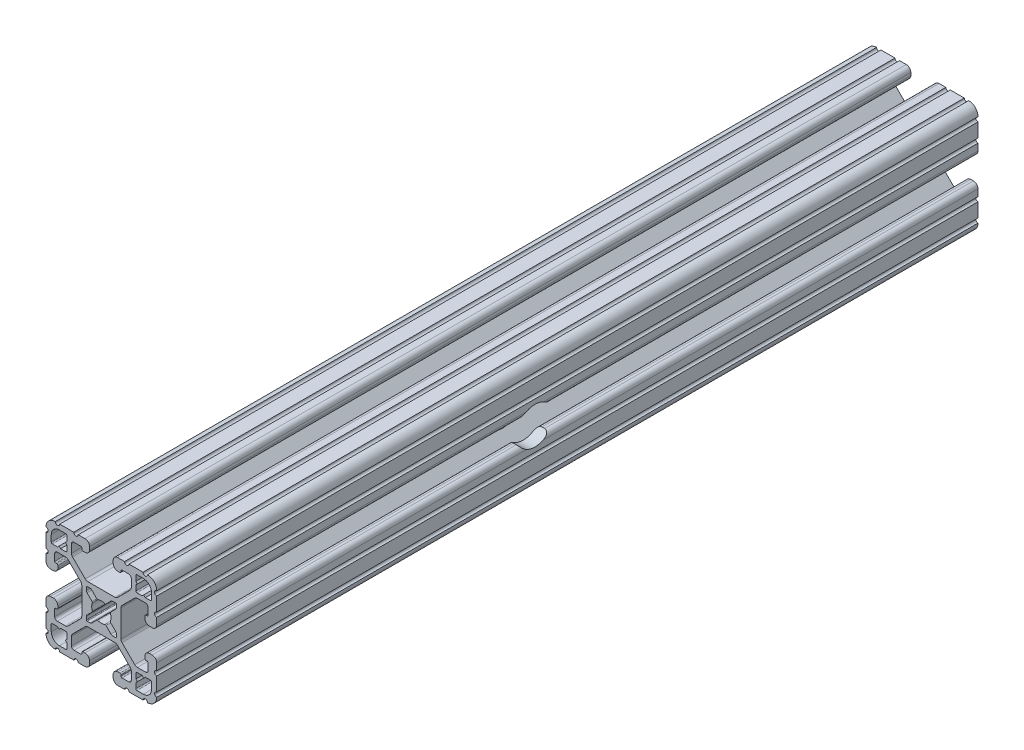
SolidWorks part; units mm, degrees
ref_plane "Front Plane" through (0, 0, 0) normal (0, 0, 1) x (1, 0, 0)
ref_plane "Top Plane" through (0, 0, 0) normal (0, 1, 0) x (1, 0, 0)
ref_plane "Right Plane" through (0, 0, 0) normal (1, 0, 0) x (0, 0, -1)
ref_plane "Plane1" through (0, 0, -2322.576) normal (0, 0, -1) x (-1, 0, 0)
sketch "Sketch1" plane through (0, 0, -2322.576) normal (0, 0, -1) x (-1, 0, 0)
  line L0 (17.2466, 14.4526) -> (17.2466, 12.2428)
  line L1 (16.8656, 11.8618) -> (15.0927, 11.8618)
  line L2 (15.0927, 11.8618) -> (14.5542, 12.4003)
  line L3 (14.5542, 12.4003) -> (14.0157, 11.8618)
  line L4 (14.0157, 11.8618) -> (12.2428, 11.8618)
  line L5 (11.8618, 12.2428) -> (11.8618, 14.0157)
  line L6 (11.8618, 14.0157) -> (12.4003, 14.5542)
  line L7 (12.4003, 14.5542) -> (11.8618, 15.0927)
  line L8 (11.8618, 15.0927) -> (11.8618, 16.8656)
  line L9 (12.2428, 17.2466) -> (14.4526, 17.2466)
  line L10 (17.2466, -12.2428) -> (17.2466, -14.4526)
  line L11 (14.4526, -17.2466) -> (12.2428, -17.2466)
  line L12 (11.8618, -16.8656) -> (11.8618, -15.0927)
  line L13 (11.8618, -15.0927) -> (12.4003, -14.5542)
  line L14 (12.4003, -14.5542) -> (11.8618, -14.0157)
  line L15 (11.8618, -14.0157) -> (11.8618, -12.2428)
  line L16 (12.2428, -11.8618) -> (14.0157, -11.8618)
  line L17 (14.0157, -11.8618) -> (14.5542, -12.4003)
  line L18 (14.5542, -12.4003) -> (15.0927, -11.8618)
  line L19 (15.0927, -11.8618) -> (16.8656, -11.8618)
  line L20 (5.1689, -3.9207) -> (5.1689, -4.9149)
  line L21 (4.9149, -5.1689) -> (3.9207, -5.1689)
  line L22 (3.2921, -4.9085) -> (1.5823, -3.1988)
  line L23 (-1.5823, -3.1988) -> (-3.2921, -4.9085)
  line L24 (-3.9207, -5.1689) -> (-4.9149, -5.1689)
  line L25 (-5.1689, -4.9149) -> (-5.1689, -3.9207)
  line L26 (-4.9085, -3.2921) -> (-3.1988, -1.5823)
  line L27 (-3.1988, 1.5823) -> (-4.9085, 3.2921)
  line L28 (-5.1689, 3.9207) -> (-5.1689, 4.9149)
  line L29 (-4.9149, 5.1689) -> (-3.9207, 5.1689)
  line L30 (-3.2921, 4.9085) -> (-1.5823, 3.1988)
  line L31 (1.5823, 3.1988) -> (3.2921, 4.9085)
  line L32 (3.9207, 5.1689) -> (4.9149, 5.1689)
  line L33 (5.1689, 4.9149) -> (5.1689, 3.9207)
  line L34 (4.9085, 3.2921) -> (3.1988, 1.5823)
  line L35 (3.1988, -1.5823) -> (4.9085, -3.2921)
  line L36 (-11.8618, -12.2428) -> (-11.8618, -14.0157)
  line L37 (-11.8618, -14.0157) -> (-12.4003, -14.5542)
  line L38 (-12.4003, -14.5542) -> (-11.8618, -15.0927)
  line L39 (-11.8618, -15.0927) -> (-11.8618, -16.8656)
  line L40 (-12.2428, -17.2466) -> (-14.4526, -17.2466)
  line L41 (-17.2466, -14.4526) -> (-17.2466, -12.2428)
  line L42 (-16.8656, -11.8618) -> (-15.0927, -11.8618)
  line L43 (-15.0927, -11.8618) -> (-14.5542, -12.4003)
  line L44 (-14.5542, -12.4003) -> (-14.0157, -11.8618)
  line L45 (-14.0157, -11.8618) -> (-12.2428, -11.8618)
  line L46 (-11.8618, 16.8656) -> (-11.8618, 15.0927)
  line L47 (-11.8618, 15.0927) -> (-12.4003, 14.5542)
  line L48 (-12.4003, 14.5542) -> (-11.8618, 14.0157)
  line L49 (-11.8618, 14.0157) -> (-11.8618, 12.2428)
  line L50 (-12.2428, 11.8618) -> (-14.0157, 11.8618)
  line L51 (-14.0157, 11.8618) -> (-14.5542, 12.4003)
  line L52 (-14.5542, 12.4003) -> (-15.0927, 11.8618)
  line L53 (-15.0927, 11.8618) -> (-16.8656, 11.8618)
  line L54 (-17.2466, 12.2428) -> (-17.2466, 14.4526)
  line L55 (-14.4526, 17.2466) -> (-12.2428, 17.2466)
  line L56 (19.05, -14.3256) -> (19.05, -9.4996)
  line L57 (19.05, -7.9756) -> (19.05, -5.6388)
  line L58 (17.4752, -4.064) -> (16.5608, -4.064)
  line L59 (14.986, -5.6388) -> (14.986, -6.35)
  line L60 (15.367, -6.731) -> (15.6972, -6.731)
  line L61 (16.0782, -7.112) -> (16.0782, -9.398)
  line L62 (15.1892, -10.287) -> (12.3756, -10.287)
  line L63 (11.4776, -9.915) -> (7.1157, -5.5531)
  line L64 (6.7437, -4.6551) -> (6.7437, 4.6551)
  line L65 (7.1157, 5.5531) -> (11.4776, 9.915)
  line L66 (12.3756, 10.287) -> (15.1892, 10.287)
  line L67 (16.0782, 9.398) -> (16.0782, 7.112)
  line L68 (15.6972, 6.731) -> (15.367, 6.731)
  line L69 (14.986, 6.35) -> (14.986, 5.6388)
  line L70 (16.5608, 4.064) -> (17.4752, 4.064)
  line L71 (19.05, 5.6388) -> (19.05, 7.9756)
  line L72 (19.05, 9.4996) -> (19.05, 14.3256)
  line L73 (14.3256, 19.05) -> (9.4996, 19.05)
  line L74 (7.9756, 19.05) -> (5.6388, 19.05)
  line L75 (4.064, 17.4752) -> (4.064, 16.5608)
  line L76 (5.6388, 14.986) -> (6.35, 14.986)
  line L77 (6.731, 15.367) -> (6.731, 15.6972)
  line L78 (7.112, 16.0782) -> (9.398, 16.0782)
  line L79 (10.287, 15.1892) -> (10.287, 12.3756)
  line L80 (9.915, 11.4776) -> (5.5531, 7.1157)
  line L81 (4.6551, 6.7437) -> (-4.6551, 6.7437)
  line L82 (-5.5531, 7.1157) -> (-9.915, 11.4776)
  line L83 (-10.287, 12.3756) -> (-10.287, 15.1892)
  line L84 (-9.398, 16.0782) -> (-7.112, 16.0782)
  line L85 (-6.731, 15.6972) -> (-6.731, 15.367)
  line L86 (-6.35, 14.986) -> (-5.6388, 14.986)
  line L87 (-4.064, 16.5608) -> (-4.064, 17.4752)
  line L88 (-5.6388, 19.05) -> (-7.9756, 19.05)
  line L89 (-9.4996, 19.05) -> (-14.3256, 19.05)
  line L90 (-19.05, 14.3256) -> (-19.05, 9.4996)
  line L91 (-19.05, 7.9756) -> (-19.05, 5.6388)
  line L92 (-17.4752, 4.064) -> (-16.5608, 4.064)
  line L93 (-14.986, 5.6388) -> (-14.986, 6.35)
  line L94 (-15.367, 6.731) -> (-15.6972, 6.731)
  line L95 (-16.0782, 7.112) -> (-16.0782, 9.398)
  line L96 (-15.1892, 10.287) -> (-12.3756, 10.287)
  line L97 (-11.4776, 9.915) -> (-7.1157, 5.5531)
  line L98 (-6.7437, 4.6551) -> (-6.7437, -4.6551)
  line L99 (-7.1157, -5.5531) -> (-11.4776, -9.915)
  line L100 (-12.3756, -10.287) -> (-15.1892, -10.287)
  line L101 (-16.0782, -9.398) -> (-16.0782, -7.112)
  line L102 (-15.6972, -6.731) -> (-15.367, -6.731)
  line L103 (-14.986, -6.35) -> (-14.986, -5.6388)
  line L104 (-16.5608, -4.064) -> (-17.4752, -4.064)
  line L105 (-19.05, -5.6388) -> (-19.05, -7.9756)
  line L106 (-19.05, -9.4996) -> (-19.05, -14.3256)
  line L107 (-14.3256, -19.05) -> (-9.4996, -19.05)
  line L108 (-7.9756, -19.05) -> (-5.6388, -19.05)
  line L109 (-4.064, -17.4752) -> (-4.064, -16.5608)
  line L110 (-5.6388, -14.986) -> (-6.35, -14.986)
  line L111 (-6.731, -15.367) -> (-6.731, -15.6972)
  line L112 (-7.112, -16.0782) -> (-9.398, -16.0782)
  line L113 (-10.287, -15.1892) -> (-10.287, -12.3756)
  line L114 (-9.915, -11.4776) -> (-5.5531, -7.1157)
  line L115 (-4.6551, -6.7437) -> (4.6551, -6.7437)
  line L116 (5.5531, -7.1157) -> (9.915, -11.4776)
  line L117 (10.287, -12.3756) -> (10.287, -15.1892)
  line L118 (9.398, -16.0782) -> (7.112, -16.0782)
  line L119 (6.731, -15.6972) -> (6.731, -15.367)
  line L120 (6.35, -14.986) -> (5.6388, -14.986)
  line L121 (4.064, -16.5608) -> (4.064, -17.4752)
  line L122 (5.6388, -19.05) -> (7.9756, -19.05)
  line L123 (9.4996, -19.05) -> (14.3256, -19.05)
  arc A0 (17.2466, 12.2428) -> (16.8656, 11.8618) centre (16.8656, 12.2428) cw
  arc A1 (12.2428, 11.8618) -> (11.8618, 12.2428) centre (12.2428, 12.2428) cw
  arc A2 (11.8618, 16.8656) -> (12.2428, 17.2466) centre (12.2428, 16.8656) cw
  arc A3 (14.4526, 17.2466) -> (17.2466, 14.4526) centre (14.4526, 14.4526) cw
  arc A4 (17.2466, -14.4526) -> (14.4526, -17.2466) centre (14.4526, -14.4526) cw
  arc A5 (12.2428, -17.2466) -> (11.8618, -16.8656) centre (12.2428, -16.8656) cw
  arc A6 (11.8618, -12.2428) -> (12.2428, -11.8618) centre (12.2428, -12.2428) cw
  arc A7 (16.8656, -11.8618) -> (17.2466, -12.2428) centre (16.8656, -12.2428) cw
  arc A8 (5.1689, -4.9149) -> (4.9149, -5.1689) centre (4.9149, -4.9149) cw
  arc A9 (3.9207, -5.1689) -> (3.2921, -4.9085) centre (3.9207, -4.2799) cw
  arc A10 (1.5823, -3.1988) -> (1.178, -3.1119) centre (1.3129, -3.4682) ccw
  arc A11 (1.178, -3.1119) -> (-1.178, -3.1119) centre (0, 0) cw
  arc A12 (-1.178, -3.1119) -> (-1.5823, -3.1988) centre (-1.3129, -3.4682) ccw
  arc A13 (-3.2921, -4.9085) -> (-3.9207, -5.1689) centre (-3.9207, -4.2799) cw
  arc A14 (-4.9149, -5.1689) -> (-5.1689, -4.9149) centre (-4.9149, -4.9149) cw
  arc A15 (-5.1689, -3.9207) -> (-4.9085, -3.2921) centre (-4.2799, -3.9207) cw
  arc A16 (-3.1988, -1.5823) -> (-3.1119, -1.178) centre (-3.4682, -1.3129) ccw
  arc A17 (-3.1119, -1.178) -> (-3.1119, 1.178) centre (0, 0) cw
  arc A18 (-3.1119, 1.178) -> (-3.1988, 1.5823) centre (-3.4682, 1.3129) ccw
  arc A19 (-4.9085, 3.2921) -> (-5.1689, 3.9207) centre (-4.2799, 3.9207) cw
  arc A20 (-5.1689, 4.9149) -> (-4.9149, 5.1689) centre (-4.9149, 4.9149) cw
  arc A21 (-3.9207, 5.1689) -> (-3.2921, 4.9085) centre (-3.9207, 4.2799) cw
  arc A22 (-1.5823, 3.1988) -> (-1.178, 3.1119) centre (-1.3129, 3.4682) ccw
  arc A23 (-1.178, 3.1119) -> (1.178, 3.1119) centre (0, 0) cw
  arc A24 (1.178, 3.1119) -> (1.5823, 3.1988) centre (1.3129, 3.4682) ccw
  arc A25 (3.2921, 4.9085) -> (3.9207, 5.1689) centre (3.9207, 4.2799) cw
  arc A26 (4.9149, 5.1689) -> (5.1689, 4.9149) centre (4.9149, 4.9149) cw
  arc A27 (5.1689, 3.9207) -> (4.9085, 3.2921) centre (4.2799, 3.9207) cw
  arc A28 (3.1988, 1.5823) -> (3.1119, 1.178) centre (3.4682, 1.3129) ccw
  arc A29 (3.1119, 1.178) -> (3.1119, -1.178) centre (0, 0) cw
  arc A30 (3.1119, -1.178) -> (3.1988, -1.5823) centre (3.4682, -1.3129) ccw
  arc A31 (4.9085, -3.2921) -> (5.1689, -3.9207) centre (4.2799, -3.9207) cw
  arc A32 (-11.8618, -16.8656) -> (-12.2428, -17.2466) centre (-12.2428, -16.8656) cw
  arc A33 (-14.4526, -17.2466) -> (-17.2466, -14.4526) centre (-14.4526, -14.4526) cw
  arc A34 (-17.2466, -12.2428) -> (-16.8656, -11.8618) centre (-16.8656, -12.2428) cw
  arc A35 (-12.2428, -11.8618) -> (-11.8618, -12.2428) centre (-12.2428, -12.2428) cw
  arc A36 (-12.2428, 17.2466) -> (-11.8618, 16.8656) centre (-12.2428, 16.8656) cw
  arc A37 (-11.8618, 12.2428) -> (-12.2428, 11.8618) centre (-12.2428, 12.2428) cw
  arc A38 (-16.8656, 11.8618) -> (-17.2466, 12.2428) centre (-16.8656, 12.2428) cw
  arc A39 (-17.2466, 14.4526) -> (-14.4526, 17.2466) centre (-14.4526, 14.4526) cw
  arc A40 (19.05, -9.4996) -> (19.05, -7.9756) centre (19.05, -8.7376) cw
  arc A41 (19.05, -5.6388) -> (17.4752, -4.064) centre (17.4752, -5.6388) ccw
  arc A42 (16.5608, -4.064) -> (14.986, -5.6388) centre (16.5608, -5.6388) ccw
  arc A43 (14.986, -6.35) -> (15.367, -6.731) centre (15.367, -6.35) ccw
  arc A44 (15.6972, -6.731) -> (16.0782, -7.112) centre (15.6972, -7.112) cw
  arc A45 (16.0782, -9.398) -> (15.1892, -10.287) centre (15.1892, -9.398) cw
  arc A46 (12.3756, -10.287) -> (11.4776, -9.915) centre (12.3756, -9.017) cw
  arc A47 (7.1157, -5.5531) -> (6.7437, -4.6551) centre (8.0137, -4.6551) cw
  arc A48 (6.7437, 4.6551) -> (7.1157, 5.5531) centre (8.0137, 4.6551) cw
  arc A49 (11.4776, 9.915) -> (12.3756, 10.287) centre (12.3756, 9.017) cw
  arc A50 (15.1892, 10.287) -> (16.0782, 9.398) centre (15.1892, 9.398) cw
  arc A51 (16.0782, 7.112) -> (15.6972, 6.731) centre (15.6972, 7.112) cw
  arc A52 (15.367, 6.731) -> (14.986, 6.35) centre (15.367, 6.35) ccw
  arc A53 (14.986, 5.6388) -> (16.5608, 4.064) centre (16.5608, 5.6388) ccw
  arc A54 (17.4752, 4.064) -> (19.05, 5.6388) centre (17.4752, 5.6388) ccw
  arc A55 (19.05, 7.9756) -> (19.05, 9.4996) centre (19.05, 8.7376) cw
  arc A56 (19.05, 14.3256) -> (19.0499, 15.8496) centre (19.05, 15.0876) cw
  arc A57 (19.0499, 15.8496) -> (15.8496, 19.0499) centre (15.875, 15.875) ccw
  arc A58 (15.8496, 19.0499) -> (14.3256, 19.05) centre (15.0876, 19.05) cw
  arc A59 (9.4996, 19.05) -> (7.9756, 19.05) centre (8.7376, 19.05) cw
  arc A60 (5.6388, 19.05) -> (4.064, 17.4752) centre (5.6388, 17.4752) ccw
  arc A61 (4.064, 16.5608) -> (5.6388, 14.986) centre (5.6388, 16.5608) ccw
  arc A62 (6.35, 14.986) -> (6.731, 15.367) centre (6.35, 15.367) ccw
  arc A63 (6.731, 15.6972) -> (7.112, 16.0782) centre (7.112, 15.6972) cw
  arc A64 (9.398, 16.0782) -> (10.287, 15.1892) centre (9.398, 15.1892) cw
  arc A65 (10.287, 12.3756) -> (9.915, 11.4776) centre (9.017, 12.3756) cw
  arc A66 (5.5531, 7.1157) -> (4.6551, 6.7437) centre (4.6551, 8.0137) cw
  arc A67 (-4.6551, 6.7437) -> (-5.5531, 7.1157) centre (-4.6551, 8.0137) cw
  arc A68 (-9.915, 11.4776) -> (-10.287, 12.3756) centre (-9.017, 12.3756) cw
  arc A69 (-10.287, 15.1892) -> (-9.398, 16.0782) centre (-9.398, 15.1892) cw
  arc A70 (-7.112, 16.0782) -> (-6.731, 15.6972) centre (-7.112, 15.6972) cw
  arc A71 (-6.731, 15.367) -> (-6.35, 14.986) centre (-6.35, 15.367) ccw
  arc A72 (-5.6388, 14.986) -> (-4.064, 16.5608) centre (-5.6388, 16.5608) ccw
  arc A73 (-4.064, 17.4752) -> (-5.6388, 19.05) centre (-5.6388, 17.4752) ccw
  arc A74 (-7.9756, 19.05) -> (-9.4996, 19.05) centre (-8.7376, 19.05) cw
  arc A75 (-14.3256, 19.05) -> (-15.8496, 19.0499) centre (-15.0876, 19.05) cw
  arc A76 (-15.8496, 19.0499) -> (-19.0499, 15.8496) centre (-15.875, 15.875) ccw
  arc A77 (-19.0499, 15.8496) -> (-19.05, 14.3256) centre (-19.05, 15.0876) cw
  arc A78 (-19.05, 9.4996) -> (-19.05, 7.9756) centre (-19.05, 8.7376) cw
  arc A79 (-19.05, 5.6388) -> (-17.4752, 4.064) centre (-17.4752, 5.6388) ccw
  arc A80 (-16.5608, 4.064) -> (-14.986, 5.6388) centre (-16.5608, 5.6388) ccw
  arc A81 (-14.986, 6.35) -> (-15.367, 6.731) centre (-15.367, 6.35) ccw
  arc A82 (-15.6972, 6.731) -> (-16.0782, 7.112) centre (-15.6972, 7.112) cw
  arc A83 (-16.0782, 9.398) -> (-15.1892, 10.287) centre (-15.1892, 9.398) cw
  arc A84 (-12.3756, 10.287) -> (-11.4776, 9.915) centre (-12.3756, 9.017) cw
  arc A85 (-7.1157, 5.5531) -> (-6.7437, 4.6551) centre (-8.0137, 4.6551) cw
  arc A86 (-6.7437, -4.6551) -> (-7.1157, -5.5531) centre (-8.0137, -4.6551) cw
  arc A87 (-11.4776, -9.915) -> (-12.3756, -10.287) centre (-12.3756, -9.017) cw
  arc A88 (-15.1892, -10.287) -> (-16.0782, -9.398) centre (-15.1892, -9.398) cw
  arc A89 (-16.0782, -7.112) -> (-15.6972, -6.731) centre (-15.6972, -7.112) cw
  arc A90 (-15.367, -6.731) -> (-14.986, -6.35) centre (-15.367, -6.35) ccw
  arc A91 (-14.986, -5.6388) -> (-16.5608, -4.064) centre (-16.5608, -5.6388) ccw
  arc A92 (-17.4752, -4.064) -> (-19.05, -5.6388) centre (-17.4752, -5.6388) ccw
  arc A93 (-19.05, -7.9756) -> (-19.05, -9.4996) centre (-19.05, -8.7376) cw
  arc A94 (-19.05, -14.3256) -> (-19.0499, -15.8496) centre (-19.05, -15.0876) cw
  arc A95 (-19.0499, -15.8496) -> (-15.8496, -19.0499) centre (-15.875, -15.875) ccw
  arc A96 (-15.8496, -19.0499) -> (-14.3256, -19.05) centre (-15.0876, -19.05) cw
  arc A97 (-9.4996, -19.05) -> (-7.9756, -19.05) centre (-8.7376, -19.05) cw
  arc A98 (-5.6388, -19.05) -> (-4.064, -17.4752) centre (-5.6388, -17.4752) ccw
  arc A99 (-4.064, -16.5608) -> (-5.6388, -14.986) centre (-5.6388, -16.5608) ccw
  arc A100 (-6.35, -14.986) -> (-6.731, -15.367) centre (-6.35, -15.367) ccw
  arc A101 (-6.731, -15.6972) -> (-7.112, -16.0782) centre (-7.112, -15.6972) cw
  arc A102 (-9.398, -16.0782) -> (-10.287, -15.1892) centre (-9.398, -15.1892) cw
  arc A103 (-10.287, -12.3756) -> (-9.915, -11.4776) centre (-9.017, -12.3756) cw
  arc A104 (-5.5531, -7.1157) -> (-4.6551, -6.7437) centre (-4.6551, -8.0137) cw
  arc A105 (4.6551, -6.7437) -> (5.5531, -7.1157) centre (4.6551, -8.0137) cw
  arc A106 (9.915, -11.4776) -> (10.287, -12.3756) centre (9.017, -12.3756) cw
  arc A107 (10.287, -15.1892) -> (9.398, -16.0782) centre (9.398, -15.1892) cw
  arc A108 (7.112, -16.0782) -> (6.731, -15.6972) centre (7.112, -15.6972) cw
  arc A109 (6.731, -15.367) -> (6.35, -14.986) centre (6.35, -15.367) ccw
  arc A110 (5.6388, -14.986) -> (4.064, -16.5608) centre (5.6388, -16.5608) ccw
  arc A111 (4.064, -17.4752) -> (5.6388, -19.05) centre (5.6388, -17.4752) ccw
  arc A112 (7.9756, -19.05) -> (9.4996, -19.05) centre (8.7376, -19.05) cw
  arc A113 (14.3256, -19.05) -> (15.8496, -19.0499) centre (15.0876, -19.05) cw
  arc A114 (15.8496, -19.0499) -> (19.0499, -15.8496) centre (15.875, -15.875) ccw
  arc A115 (19.0499, -15.8496) -> (19.05, -14.3256) centre (19.05, -15.0876) cw
extrude "Boss-Extrude1" add sketch "Sketch1" against normal blind 282.575
sketch "Sketch2" plane through (19.05, 0, 0) normal (1, 0, 0) x (0, 0, -1)
  line L0 (2322.576, 4.6551) -> (2322.576, -4.6551) construction
  circle A0 centre (2170.176, 0) radius 6.35
  dimension "D1" = 152.4
extrude "Cut-Extrude1" cut sketch "Sketch2" against normal through all
